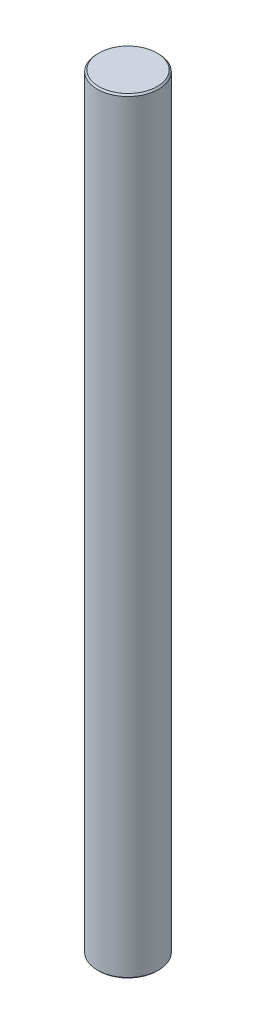
SolidWorks part; units mm, degrees
ref_plane "Front Plane" through (0, 0, 0) normal (0, 0, 1) x (1, 0, 0)
ref_plane "Top Plane" through (0, 0, 0) normal (0, 1, 0) x (1, 0, 0)
ref_plane "Right Plane" through (0, 0, 0) normal (1, 0, 0) x (0, 0, -1)
sketch "Sketch1" plane through (0, 0, 0) normal (0, 1, 0) x (1, 0, 0)
  circle A0 centre (0, 0) radius 4
  dimension "D1" = 8
extrude "Boss-Extrude1" add sketch "Sketch1" along normal blind 100
chamfer "Chamfer1" distance 0.2 angle 45 2 edges at (0, 0, 4) (0, 100, 4)
